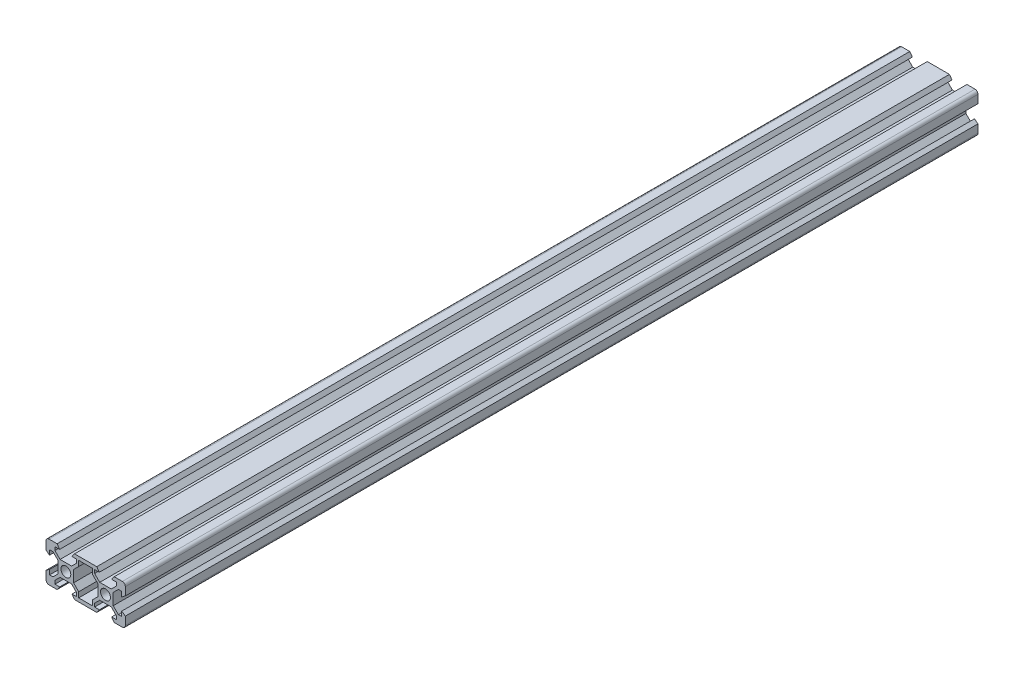
SolidWorks part; units mm, degrees
ref_plane "前视基准面" through (0, 0, 0) normal (0, 0, 1) x (1, 0, 0)
ref_plane "上视基准面" through (0, 0, 0) normal (0, 1, 0) x (1, 0, 0)
ref_plane "右视基准面" through (0, 0, 0) normal (1, 0, 0) x (0, 0, -1)
sketch "草图1" plane through (0, 0, 0) normal (0, 0, 1) x (1, 0, 0)
  line L0 (16.8101, 19.3214) -> (19.4, 21.9114) construction
  line L1 (14.8, 34.8214) -> (18.9, 34.8214)
  line L2 (13.3, 33.3214) -> (13.3, 29.2214)
  line L3 (14.8, 14.8214) -> (18.9, 14.8214)
  line L5 (36.8101, 19.3214) -> (39.4, 21.9114) construction
  line L7 (27.2, 27.7315) -> (29.7899, 30.3214) construction
  line L9 (28.8, 31.3114) -> (26.2101, 28.7214)
  line L12 (26.2101, 28.7214) -> (28.8, 31.3114) construction
  line L13 (27.2, 27.7315) -> (29.7899, 30.3214)
  line L15 (20.3899, 28.7214) -> (26.2101, 28.7214) construction
  line L17 (53.3, 33.3214) -> (53.3, 29.2214)
  line L18 (18.9, 34.8214) -> (20.2, 33.0214)
  line L19 (27.7, 34.8214) -> (26.4, 33.0214)
  line L20 (26.4, 33.0214) -> (28.8, 33.0214)
  line L21 (28.8, 33.0214) -> (28.8, 31.3114)
  line L22 (26.2101, 28.7214) -> (20.3899, 28.7214)
  line L23 (47.2, 27.7315) -> (49.7899, 30.3214) construction
  line L24 (53.3, 29.2214) -> (51.5, 27.9214)
  line L25 (20.3899, 28.7214) -> (17.8, 31.3114)
  line L26 (17.8, 31.3114) -> (17.8, 33.0214)
  line L27 (17.8, 33.0214) -> (20.2, 33.0214)
  line L28 (27.2, 21.9114) -> (27.2, 27.7315)
  line L29 (29.7899, 19.3214) -> (27.2, 21.9114)
  line L33 (27.7, 14.8214) -> (26.4, 16.6214)
  line L34 (28.8, 16.6214) -> (26.4, 16.6214)
  line L35 (28.8, 18.3315) -> (28.8, 16.6214)
  line L36 (26.2101, 20.9214) -> (28.8, 18.3315)
  line L37 (20.3899, 20.9214) -> (26.2101, 20.9214)
  line L38 (17.8, 18.3315) -> (20.3899, 20.9214)
  line L39 (17.8, 16.6214) -> (17.8, 18.3315)
  line L40 (20.2, 16.6214) -> (17.8, 16.6214)
  line L41 (18.9, 14.8214) -> (20.2, 16.6214)
  line L42 (13.3, 20.4214) -> (15.1, 21.7214)
  line L43 (15.1, 19.3214) -> (15.1, 21.7214)
  line L44 (16.8101, 19.3214) -> (15.1, 19.3214)
  line L45 (19.4, 21.9114) -> (16.8101, 19.3214)
  line L46 (19.4, 27.7315) -> (19.4, 21.9114)
  line L47 (16.8101, 30.3214) -> (19.4, 27.7315)
  line L48 (15.1, 30.3214) -> (16.8101, 30.3214)
  line L49 (15.1, 27.9214) -> (15.1, 30.3214)
  line L50 (13.3, 29.2214) -> (15.1, 27.9214)
  line L53 (13.3, 20.4214) -> (13.3, 16.3214)
  line L55 (48.8, 31.3114) -> (46.2101, 28.7214)
  line L56 (51.5, 30.3214) -> (51.5, 27.9214)
  line L57 (49.7899, 30.3214) -> (51.5, 30.3214)
  line L58 (46.2101, 28.7214) -> (48.8, 31.3114) construction
  line L59 (47.2, 27.7315) -> (49.7899, 30.3214)
  line L60 (40.3899, 28.7214) -> (46.2101, 28.7214) construction
  line L61 (38.9, 34.8214) -> (40.2, 33.0214)
  line L62 (47.7, 34.8214) -> (46.4, 33.0214)
  line L63 (46.4, 33.0214) -> (48.8, 33.0214)
  line L64 (48.8, 33.0214) -> (48.8, 31.3114)
  line L65 (46.2101, 28.7214) -> (40.3899, 28.7214)
  line L66 (40.3899, 28.7214) -> (37.8, 31.3114)
  line L67 (37.8, 31.3114) -> (37.8, 33.0214)
  line L68 (37.8, 33.0214) -> (40.2, 33.0214)
  line L69 (47.2, 21.9114) -> (47.2, 27.7315)
  line L70 (49.7899, 19.3214) -> (47.2, 21.9114)
  line L71 (51.5, 19.3214) -> (49.7899, 19.3214)
  line L72 (51.5, 21.7214) -> (51.5, 19.3214)
  line L73 (53.3, 20.4214) -> (51.5, 21.7214)
  line L74 (47.7, 14.8214) -> (46.4, 16.6214)
  line L75 (48.8, 16.6214) -> (46.4, 16.6214)
  line L76 (48.8, 18.3315) -> (48.8, 16.6214)
  line L77 (46.2101, 20.9214) -> (48.8, 18.3315)
  line L78 (40.3899, 20.9214) -> (46.2101, 20.9214)
  line L79 (37.8, 18.3315) -> (40.3899, 20.9214)
  line L80 (37.8, 16.6214) -> (37.8, 18.3315)
  line L81 (40.2, 16.6214) -> (37.8, 16.6214)
  line L82 (38.9, 14.8214) -> (40.2, 16.6214)
  line L86 (39.4, 21.9114) -> (36.8101, 19.3214)
  line L87 (39.4, 27.7315) -> (39.4, 21.9114)
  line L88 (36.8101, 30.3214) -> (39.4, 27.7315)
  line L92 (47.7, 34.8214) -> (51.8, 34.8214)
  line L93 (53.3, 20.4214) -> (53.3, 16.3214)
  line L95 (47.7, 14.8214) -> (51.8, 14.8214)
  line L96 (31.5, 19.3214) -> (29.7899, 19.3214) [skipped]
  line L97 (31.5, 21.7214) -> (31.5, 19.3214) [skipped]
  line L98 (33.3, 20.4214) -> (31.5, 21.7214) [skipped]
  line L99 (29.7899, 30.3214) -> (31.5, 30.3214) [skipped]
  line L100 (33.3, 29.2214) -> (31.5, 27.9214) [skipped]
  line L101 (31.5, 30.3214) -> (31.5, 27.9214) [skipped]
  line L102 (27.7, 14.8214) -> (38.9, 14.8214)
  line L103 (29.7899, 16.6214) -> (36.8101, 16.6214)
  line L104 (36.8101, 16.6214) -> (36.8101, 19.3214)
  line L105 (29.7899, 16.6214) -> (29.7899, 19.3214)
  line L106 (27.7, 34.8214) -> (38.9, 34.8214)
  line L107 (36.8101, 33.0214) -> (29.7899, 33.0214)
  line L108 (29.7899, 33.0214) -> (29.7899, 30.3214)
  line L109 (36.8101, 30.3214) -> (36.8101, 33.0214)
  circle A0 centre (23.3, 24.8214) radius 2.5
  arc A1 (14.8, 34.8214) -> (13.3, 33.3214) centre (14.8, 33.3214) ccw
  arc A4 (14.8, 14.8214) -> (13.3, 16.3214) centre (14.8, 16.3214) cw
  circle A5 centre (43.3, 24.8214) radius 2.5
  arc A7 (53.3, 33.3214) -> (51.8, 34.8214) centre (51.8, 33.3214) ccw
  arc A8 (51.8, 14.8214) -> (53.3, 16.3214) centre (51.8, 16.3214) ccw
  point P11 (33.3, 34.8214)
  point P18 (33.3, 14.8214)
  dimension "D3" = 5
  dimension "D1" = 1.5
  dimension "D7" = 1.5
  dimension "D2" = 20
  dimension "D6" = 4
extrude "凸台-拉伸1" add sketch "草图1" along normal blind 430
ref_plane "基准面1" through (27.2, 21.9114, 430) normal (0, 0, -1) x (-1, 0, 0)
sketch "草图3" plane through (0, 0, 430) normal (0, 0, 1) x (1, 0, 0)
